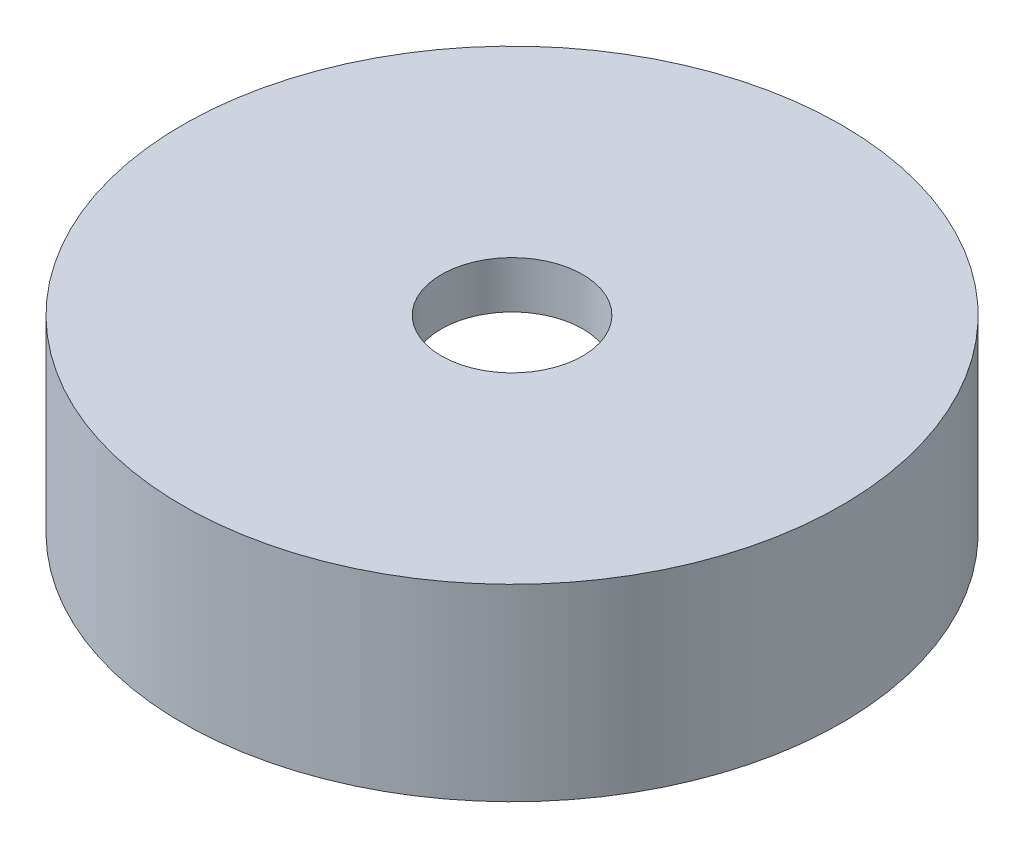
SolidWorks part; units mm, degrees
material "Alloy Steel (SS)"
ref_plane "Front Plane" through (0, 0, 0) normal (0, 0, 1) x (1, 0, 0)
ref_plane "Top Plane" through (0, 0, 0) normal (0, 1, 0) x (1, 0, 0)
ref_plane "Right Plane" through (0, 0, 0) normal (1, 0, 0) x (0, 0, -1)
sketch "Sketch1" plane through (0, 0, 0) normal (0, 0, 1) x (1, 0, 0)
  line L0 (0, 0) -> (0, 3) construction
  line L1 (0, 3) -> (6, 3)
  line L2 (6, 3) -> (6, 0)
  line L3 (0, 4) -> (7, 4)
  line L4 (7, 4) -> (7, 0)
  line L5 (0, 4) -> (0, 3)
  line L6 (6, 0) -> (7, 0)
  dimension "D1" = 6
  dimension "D2" = 3
  dimension "D3" = 1
revolve "Revolve1" add sketch "Sketch1" angle 360 about L0
hole_wizard "Ø3.0mm Dowel Hole1" positions "Sketch2" profile "Sketch3" hole size "Ø3.0" standard "ISO"
sketch "Sketch2" plane through (0, 4, 0) normal (0, 1, 0) x (1, 0, 0)
  point P0 (0, 0)
sketch "Sketch3" plane through (0, 4, 0) normal (1, 0, 0) x (0, 0, 1)
  line L0 (0, 0) -> (0, 8.5)
  line L1 (0, 8.5) -> (1.5, 7.5987)
  line L2 (1.5, 7.5987) -> (1.5, 0)
  line L5 (1.5, 0) -> (0, 0)
  line L10 (0, 8.5) -> (-1.5, 7.5987) construction
  line L11 (0, -6.35) -> (0, 107.95) construction
  dimension "Hole Dia." = 3
  dimension "Hole Depth" = 8.5
  dimension "Drill Angle" = 118
